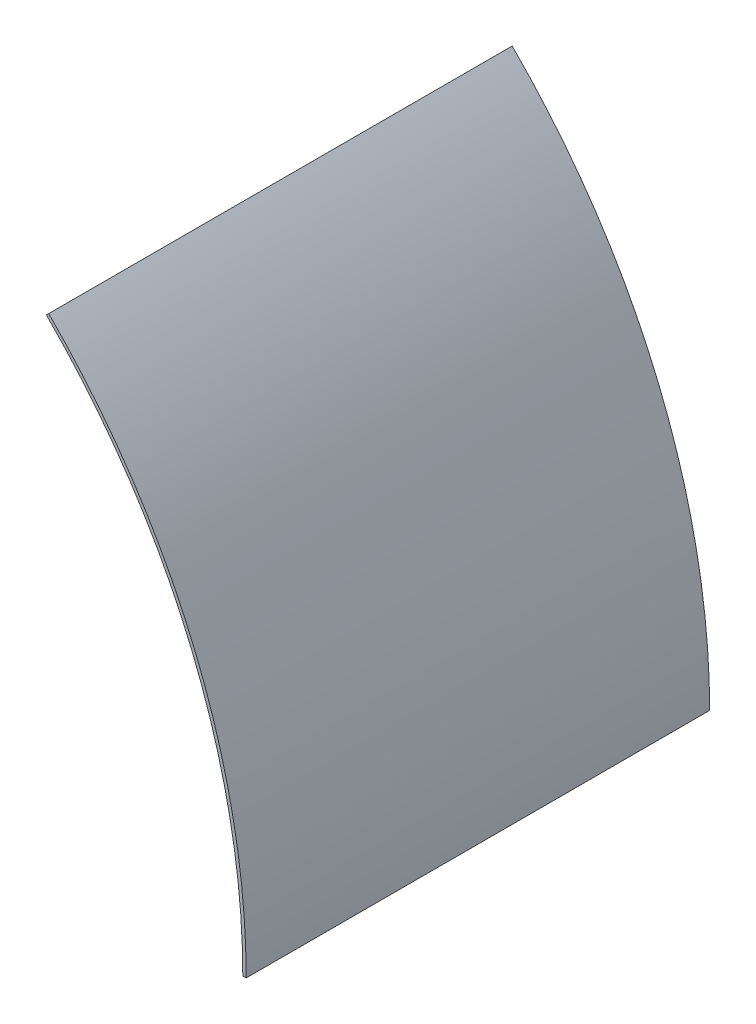
SolidWorks part; units mm, degrees
ref_plane "Front Plane" through (0, 0, 0) normal (0, 0, 1) x (1, 0, 0)
ref_plane "Top Plane" through (0, 0, 0) normal (0, 1, 0) x (1, 0, 0)
ref_plane "Right Plane" through (0, 0, 0) normal (1, 0, 0) x (0, 0, -1)
sketch "Sketch1" plane through (0, 0, 0) normal (0, 0, 1) x (1, 0, 0)
  line L0 (0, 0) -> (15.1377, 15.1377) construction
  line L1 (0, 0) -> (17.3644, 0) construction
  line L2 (179.6051, 179.6051) -> (178.7071, 178.7071)
  line L3 (254, 0) -> (252.73, 0)
  line L4 (0, 0) -> (258.0093, 0) construction
  line L5 (0, 0) -> (181.4442, 181.4442) construction
  arc A0 (179.6051, 179.6051) -> (254, 0) centre (0, 0) cw
  arc A1 (178.7071, 178.7071) -> (252.73, 0) centre (0, 0) cw
  dimension "D1" = 1.27
  dimension "D2" = 252.73
  dimension "D3" = 45
extrude "Boss-Extrude1" add sketch "Sketch1" along normal blind 174.625
equation "\"a\"= 10"
